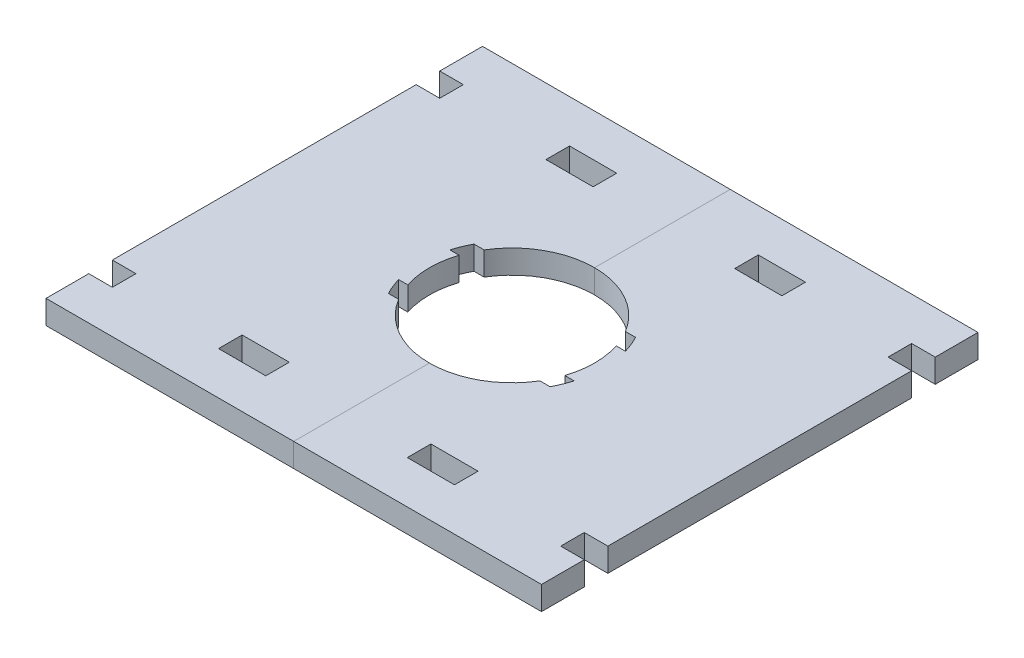
SolidWorks part; units mm, degrees
ref_plane "Front Plane" through (0, 0, 0) normal (0, 0, 1) x (1, 0, 0)
ref_plane "Top Plane" through (0, 0, 0) normal (0, 1, 0) x (1, 0, 0)
ref_plane "Right Plane" through (0, 0, 0) normal (1, 0, 0) x (0, 0, -1)
sketch "Sketch1" plane through (0, 0, 0) normal (0, 1, 0) x (1, 0, 0)
  line L0 (-15.5, 7.25) -> (-13.6999, 7.25) construction
  line L1 (-13.6999, -7.25) -> (-11.9765, -7.25)
  line L2 (-15.5, -7.25) -> (-15.5, -4.35) construction
  line L3 (-13.6999, 7.25) -> (-11.9765, 7.25)
  line L4 (15.5, 4.35) -> (15.5, 7.25) construction
  line L5 (-14.04, -6.5671) -> (-12.6813, -5.9316) construction
  line L6 (-14.04, 6.5671) -> (-12.6813, 5.9316) construction
  line L7 (-14.8771, -4.35) -> (-13.307, -4.35)
  line L8 (-15.5, -4.35) -> (-15.5, 0) construction
  line L9 (-14.8771, 4.35) -> (-13.307, 4.35)
  line L10 (15.5, 0) -> (15.5, 4.35) construction
  line L11 (-14.9234, -4.1882) -> (14.9234, 4.1882) construction
  line L12 (-14.9234, 4.1882) -> (14.9234, -4.1882) construction
  line L13 (-15.5, 7.25) -> (-14.04, 6.5671) construction
  line L14 (-15.5, 4.35) -> (-15.5, 7.25) construction
  line L15 (-15.5, 4.35) -> (-14.8771, 4.35) construction
  line L16 (-15.5, 4.35) -> (-14.9234, 4.1882) construction
  line L17 (-15.5, 0) -> (-15.5, 4.35) construction
  line L18 (-15.5, 0) -> (-15.5, 4.35) construction
  line L19 (-15.5, -4.35) -> (-15.5, 0) construction
  line L20 (-15.5, -4.35) -> (-14.9234, -4.1882) construction
  line L21 (-15.5, -4.35) -> (-14.8771, -4.35) construction
  line L22 (-15.5, -7.25) -> (-14.04, -6.5671) construction
  line L23 (-15.5, -7.25) -> (-13.6999, -7.25) construction
  line L24 (15.5, -7.25) -> (15.5, -4.35) construction
  line L25 (14.04, -6.5671) -> (15.5, -7.25) construction
  line L26 (13.6999, -7.25) -> (15.5, -7.25) construction
  line L27 (15.5, -4.35) -> (15.5, 0) construction
  line L28 (15.5, -4.35) -> (15.5, 0) construction
  line L29 (15.5, 0) -> (15.5, 4.35) construction
  line L30 (14.9234, 4.1882) -> (15.5, 4.35) construction
  line L31 (14.8771, 4.35) -> (15.5, 4.35) construction
  line L32 (13.6999, 7.25) -> (15.5, 7.25) construction
  line L33 (14.9234, -4.1882) -> (15.5, -4.35) construction
  line L34 (14.8771, -4.35) -> (15.5, -4.35) construction
  line L35 (-11.9765, 7.25) -> (11.9765, 7.25) construction
  line L36 (11.9765, 7.25) -> (13.6999, 7.25)
  line L37 (-9.3, 4.35) -> (9.3, 4.35) construction
  line L38 (13.307, 4.35) -> (14.8771, 4.35)
  line L39 (-12.6813, 5.9316) -> (-9.3, 4.35) construction
  line L40 (-9.3, 4.35) -> (9.3, -4.35) construction
  line L41 (-13.307, 4.35) -> (-9.3, 4.35) construction
  line L42 (-11.9765, -7.25) -> (11.9765, -7.25) construction
  line L43 (11.9765, -7.25) -> (13.6999, -7.25)
  line L44 (-9.3, -4.35) -> (9.3, -4.35) construction
  line L45 (13.307, -4.35) -> (14.8771, -4.35)
  line L46 (-12.6813, -5.9316) -> (-9.3, -4.35) construction
  line L47 (-9.3, -4.35) -> (9.3, 4.35) construction
  line L48 (-13.307, -4.35) -> (-9.3, -4.35) construction
  line L49 (9.3, -4.35) -> (13.307, -4.35) construction
  line L50 (9.3, -4.35) -> (12.6813, -5.9316) construction
  line L51 (12.6813, -5.9316) -> (14.04, -6.5671) construction
  line L52 (9.3, 4.35) -> (13.307, 4.35) construction
  line L53 (9.3, 4.35) -> (12.6813, 5.9316) construction
  line L54 (12.6813, 5.9316) -> (15.5, 7.25) construction
  arc A0 (-13.307, 4.35) -> (-13.307, -4.35) centre (0, 0) ccw
  arc A1 (-13.6999, 7.25) -> (-14.9234, 4.1882) centre (0, 0) ccw
  arc A2 (13.6999, 7.25) -> (-13.6999, 7.25) centre (0, 0) ccw construction
  arc A3 (-13.6999, -7.25) -> (13.6999, -7.25) centre (0, 0) ccw construction
  arc A4 (13.6999, -7.25) -> (14.9234, -4.1882) centre (0, 0) ccw
  arc A5 (15.5, 0) -> (14.9234, 4.1882) centre (0, 0) ccw construction
  arc A6 (14.9234, 4.1882) -> (13.6999, 7.25) centre (0, 0) ccw
  arc A7 (14.9234, -4.1882) -> (15.5, 0) centre (0, 0) ccw construction
  arc A8 (-14.9234, 4.1882) -> (-15.5, 0) centre (0, 0) ccw construction
  arc A9 (-14.9234, -4.1882) -> (-13.6999, -7.25) centre (0, 0) ccw
  arc A10 (-15.5, 0) -> (-14.9234, -4.1882) centre (0, 0) ccw construction
  arc A11 (-11.9765, 7.25) -> (-12.6813, 5.9316) centre (0, 0) ccw construction
  arc A12 (-12.6813, 5.9316) -> (-13.307, 4.35) centre (0, 0) ccw construction
  arc A13 (-12.6813, -5.9316) -> (-11.9765, -7.25) centre (0, 0) ccw construction
  arc A14 (-11.9765, -7.25) -> (11.9765, -7.25) centre (0, 0) ccw
  arc A15 (-13.307, -4.35) -> (-12.6813, -5.9316) centre (0, 0) ccw construction
  arc A16 (12.6813, -5.9316) -> (13.307, -4.35) centre (0, 0) ccw construction
  arc A17 (13.307, -4.35) -> (-11.9765, 7.25) centre (0, 0) ccw
  arc A18 (11.9765, -7.25) -> (12.6813, -5.9316) centre (0, 0) ccw construction
  dimension "D1" = 28
  dimension "D2" = 31
  dimension "D3" = 14.5
  dimension "D4" = 8.7
sketch "Sketch2" plane through (0, 0, 0) normal (0, 1, 0) x (1, 0, 0)
  line L0 (13.307, -4.35) -> (14.8771, -4.35) construction
  line L1 (-13.6999, 7.25) -> (-11.9765, 7.25) construction
  line L2 (-14.8771, -4.35) -> (-13.307, -4.35) construction
  line L3 (-14.8771, 4.35) -> (-13.307, 4.35) construction
  line L4 (11.9765, -7.25) -> (13.6999, -7.25) construction
  line L5 (-13.6999, -7.25) -> (-11.9765, -7.25) construction
  line L6 (11.9765, 7.25) -> (13.6999, 7.25) construction
  line L7 (13.307, 4.35) -> (14.8771, 4.35) construction
  line L8 (13.307, -4.35) -> (14.8771, -4.35)
  line L9 (-13.6999, 7.25) -> (-11.9765, 7.25)
  line L10 (-14.8771, -4.35) -> (-13.307, -4.35)
  line L11 (-14.8771, 4.35) -> (-13.307, 4.35)
  line L12 (11.9765, -7.25) -> (13.6999, -7.25)
  line L13 (-13.6999, -7.25) -> (-11.9765, -7.25)
  line L14 (11.9765, 7.25) -> (13.6999, 7.25)
  line L15 (13.307, 4.35) -> (14.8771, 4.35)
  line L17 (-42, -37) -> (42, -37)
  line L18 (-42, -37) -> (-42, 37)
  line L19 (-42, 37) -> (42, 37)
  line L20 (42, -37) -> (42, 37)
  line L21 (-42, -37) -> (42, 37) construction
  line L22 (-42, 37) -> (42, -37) construction
  arc A0 (13.307, -4.35) -> (-11.9765, 7.25) centre (0, 0) ccw construction
  arc A1 (-13.6999, 7.25) -> (-14.9234, 4.1882) centre (0, 0) ccw construction
  arc A2 (-13.307, 4.35) -> (-13.307, -4.35) centre (0, 0) ccw construction
  arc A3 (13.6999, -7.25) -> (14.9234, -4.1882) centre (0, 0) ccw construction
  arc A4 (-11.9765, -7.25) -> (11.9765, -7.25) centre (0, 0) ccw construction
  arc A5 (-14.9234, -4.1882) -> (-13.6999, -7.25) centre (0, 0) ccw construction
  arc A6 (14.9234, 4.1882) -> (13.6999, 7.25) centre (0, 0) ccw construction
  arc A7 (13.307, -4.35) -> (-11.9765, 7.25) centre (0, 0) ccw
  arc A8 (-13.6999, 7.25) -> (-14.9234, 4.1882) centre (0, 0) ccw
  arc A9 (-13.307, 4.35) -> (-13.307, -4.35) centre (0, 0) ccw
  arc A10 (13.6999, -7.25) -> (14.9234, -4.1882) centre (0, 0) ccw
  arc A11 (-11.9765, -7.25) -> (11.9765, -7.25) centre (0, 0) ccw
  arc A12 (-14.9234, -4.1882) -> (-13.6999, -7.25) centre (0, 0) ccw
  arc A13 (14.9234, 4.1882) -> (13.6999, 7.25) centre (0, 0) ccw
  dimension "D1" = 84
  dimension "D2" = 74
extrude "Boss-Extrude1" add sketch "Sketch2" along normal blind 4
split "Split1" trim tools "Right Plane" bodies to split 101 resulting bodies 102 103
sketch "Sketch4" plane through (0, 4, 0) normal (0, 1, 0) x (1, 0, 0)
  line L0 (0, -18.5) -> (42, -18.5) construction
  line L2 (42, -37) -> (42, 37) construction
  line L3 (0, -18.5) -> (0, -37) construction
  line L4 (-42, -37) -> (-42, 37) construction
  line L5 (-20, -29.75) -> (-12, -29.75)
  line L6 (-20, -29.75) -> (-20, -25.75)
  line L7 (-20, -25.75) -> (-12, -25.75)
  line L8 (-12, -29.75) -> (-12, -25.75)
  line L9 (-20, -29.75) -> (-12, -25.75) construction
  line L10 (-20, -25.75) -> (-12, -29.75) construction
  line L11 (-42, -29.75) -> (-38, -29.75)
  line L12 (-42, -29.75) -> (-42, -25.75)
  line L13 (-42, -25.75) -> (-38, -25.75)
  line L14 (-38, -29.75) -> (-38, -25.75)
  line L15 (-42, -29.75) -> (-38, -25.75) construction
  line L16 (-42, -25.75) -> (-38, -29.75) construction
  line L17 (0, 0) -> (0, -37) construction
  line L18 (-14.9234, 4.1882) -> (14.9234, -4.1882) construction
  line L33 (42, -25.75) -> (38, -29.75) construction
  line L34 (42, -29.75) -> (38, -25.75) construction
  line L35 (20, -25.75) -> (12, -29.75) construction
  line L36 (20, -29.75) -> (12, -25.75) construction
  line L45 (38, -29.75) -> (38, -25.75)
  line L46 (42, -25.75) -> (38, -25.75)
  line L47 (42, -29.75) -> (42, -25.75)
  line L48 (42, -29.75) -> (38, -29.75)
  line L49 (12, -29.75) -> (12, -25.75)
  line L50 (20, -25.75) -> (12, -25.75)
  line L51 (20, -29.75) -> (20, -25.75)
  line L52 (20, -29.75) -> (12, -29.75)
  line L53 (-2.2, 0) -> (2.2, 0) construction
  line L54 (20, 29.75) -> (12, 25.75) construction
  line L55 (20, 25.75) -> (12, 29.75) construction
  line L56 (42, 29.75) -> (38, 25.75) construction
  line L57 (42, 25.75) -> (38, 29.75) construction
  line L58 (20, 29.75) -> (12, 29.75)
  line L59 (20, 29.75) -> (20, 25.75)
  line L60 (20, 25.75) -> (12, 25.75)
  line L61 (12, 29.75) -> (12, 25.75)
  line L62 (42, 29.75) -> (38, 29.75)
  line L63 (42, 29.75) -> (42, 25.75)
  line L64 (42, 25.75) -> (38, 25.75)
  line L65 (38, 29.75) -> (38, 25.75)
  line L82 (-42, 25.75) -> (-38, 29.75) construction
  line L83 (-42, 29.75) -> (-38, 25.75) construction
  line L84 (-20, 25.75) -> (-12, 29.75) construction
  line L85 (-20, 29.75) -> (-12, 25.75) construction
  line L94 (-38, 29.75) -> (-38, 25.75)
  line L95 (-42, 25.75) -> (-38, 25.75)
  line L96 (-42, 29.75) -> (-42, 25.75)
  line L97 (-42, 29.75) -> (-38, 29.75)
  line L98 (-12, 29.75) -> (-12, 25.75)
  line L99 (-20, 25.75) -> (-12, 25.75)
  line L100 (-20, 29.75) -> (-20, 25.75)
  line L101 (-20, 29.75) -> (-12, 29.75)
  point P6 (-16, -27.75)
  point P14 (0, -27.75)
  point P15 (-40, -27.75)
  point P53 (40, -27.75)
  point P54 (16, -27.75)
  point P65 (16, 27.75)
  point P66 (40, 27.75)
  point P95 (-40, 27.75)
  point P96 (-16, 27.75)
  dimension "D1" = 4
  dimension "D2" = 8
  dimension "D3" = 20
  dimension "D4" = 4
extrude "Cut-Extrude2" cut sketch "Sketch4" against normal through all both
equation "\"m3_hole\"= 3.5"
equation "\"m3_washer\"= 7.3"
equation "\"m3_nut\"= 5.3"
equation "\"guide_width\"= 10.0"
equation "\"guide_length\"= 65.0"
equation "\"guide_tab_length\" = 10.0"
equation "\"guide_tab_width\" = 9.0"
equation "\"guide_thickness\" = 12.0"
equation "\"grinder_od\"= 52.0"
equation "\"grinder_id\"= 45.5"
equation "\"grinder_adjust_od\" = 58.0"
equation "\"funnel_width_from_adjust_ring\" = 13.0"
equation "\"drill_contact_diameter_small\" = 24.0"
equation "\"drill_contact_diameter_medium\" = 28.0"
equation "\"drill_contact_diameter_large\" = 39.0"
equation "\"drill_contact_diameter_tab\" = 31.0"
equation "\"drill_contact_ow_tab\" = 14.5"
equation "\"drill_contact_iw_tab\" = 8.7"
equation "\"drill_contact_small_height\" = 15.5"
equation "\"drill_contact_large_height\" = 34.5"
equation "\"D1@Sketch1\"=\"drill_contact_diameter_medium\""
equation "\"D2@Sketch1\"=\"drill_contact_diameter_tab\""
equation "\"D3@Sketch1\"=\"drill_contact_ow_tab\""
equation "\"D1@Sketch2\"=\"grinder_od\"+\"guide_thickness\"+20"
equation "\"D2@Sketch2\"=\"grinder_od\"+\"guide_thickness\"+\"guide_tab_length\""
equation "\"plywood_thickness\" = 3.85"
equation "\"D4@Sketch1\"=\"drill_contact_iw_tab\""
equation "\"plywood_peg_length\" = 40"
equation "\"plywood_peg_width\" = 8.0"
equation "\"D3@Sketch4\"=\"plywood_peg_length\"/2"
equation "\"D2@Sketch4\"=\"plywood_peg_width\""
